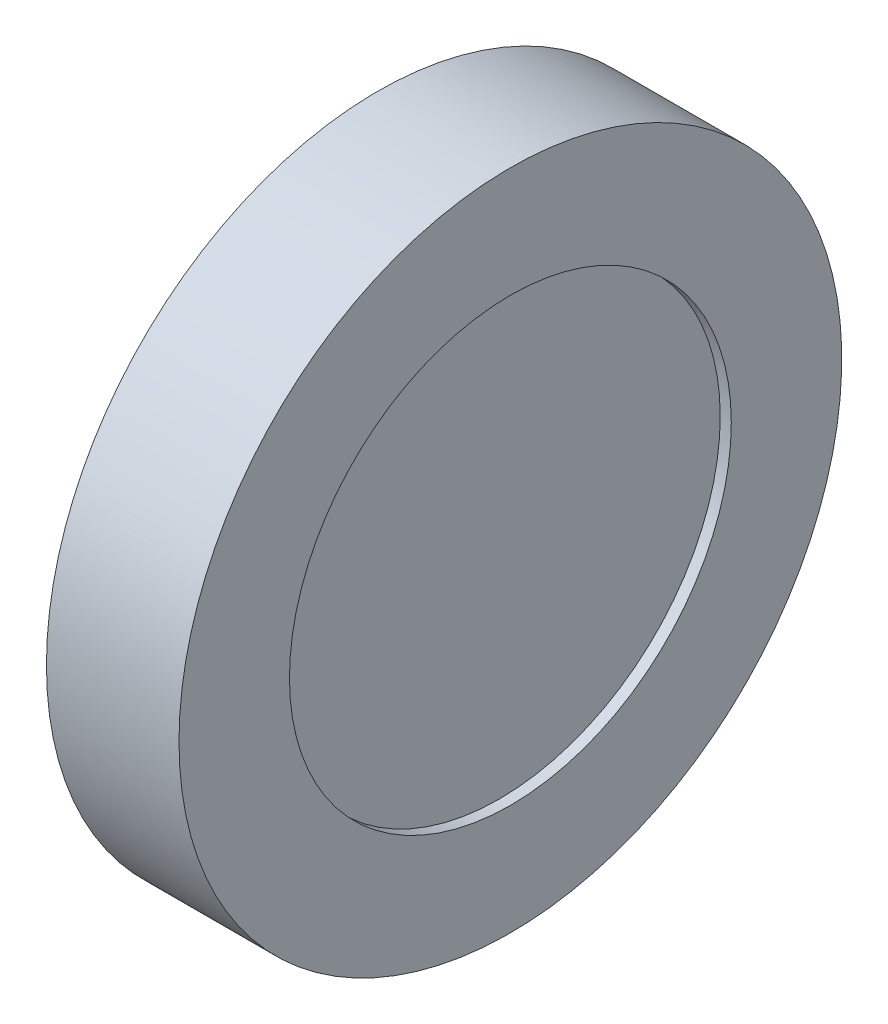
SolidWorks part; units mm, degrees
ref_plane "前视基准面" through (0, 0, 0) normal (0, 0, 1) x (1, 0, 0)
ref_plane "上视基准面" through (0, 0, 0) normal (0, 1, 0) x (1, 0, 0)
ref_plane "右视基准面" through (0, 0, 0) normal (1, 0, 0) x (0, 0, -1)
sketch "草图1" plane through (0, 0, 0) normal (0, 0, 1) x (1, 0, 0)
  line L0 (-2.5, 10) -> (-2.5, 0)
  line L2 (-2.5, 10) -> (2.5, 10)
  line L3 (-2.5, 0) -> (2.5, 0)
  line L4 (2.5, 10) -> (2.5, 0)
revolve "旋转2" add sketch "草图1" angle 360 about L3
sketch "草图4" plane through (0, 0, 0) normal (0, 0, 1) x (1, 0, 0)
  line L0 (-3, 15) -> (3, 15)
  line L1 (3, 15) -> (3, 10)
  line L2 (3, 10) -> (-3, 10)
  line L3 (2.5, 10) -> (-2.5, 10) construction
  line L4 (-3, 10) -> (-3, 15)
  line L5 (0, 10) -> (0, 15) construction
  line L6 (-1.6142, 0) -> (1.5903, 0) construction
revolve "旋转3" add sketch "草图4" angle 360 about L6
equation "\"D1@草图4\"=\"D1@草图1\""
